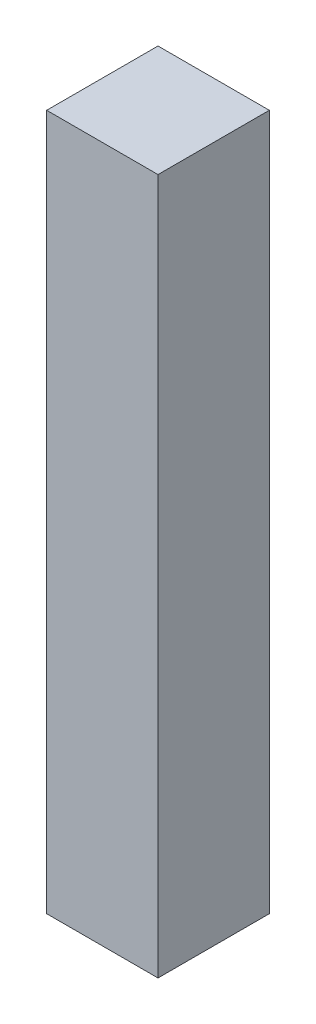
SolidWorks part; units mm, degrees
ref_plane "Front Plane" through (0, 0, 0) normal (0, 0, 1) x (1, 0, 0)
ref_plane "Top Plane" through (0, 0, 0) normal (0, 1, 0) x (1, 0, 0)
ref_plane "Right Plane" through (0, 0, 0) normal (1, 0, 0) x (0, 0, -1)
sketch "Sketch1" plane through (0, 0, 0) normal (0, 0, 1) x (1, 0, 0)
  line L1 (-20, -125) -> (20, -125)
  line L2 (-20, -125) -> (-20, 125)
  line L3 (-20, 125) -> (20, 125)
  line L4 (20, -125) -> (20, 125)
  line L5 (-20, -125) -> (20, 125) construction
  line L6 (-20, 125) -> (20, -125) construction
  point P0 (0, 0)
  dimension "D1" = 250
  dimension "D2" = 40
extrude "Boss-Extrude1" add sketch "Sketch1" along normal blind 40
